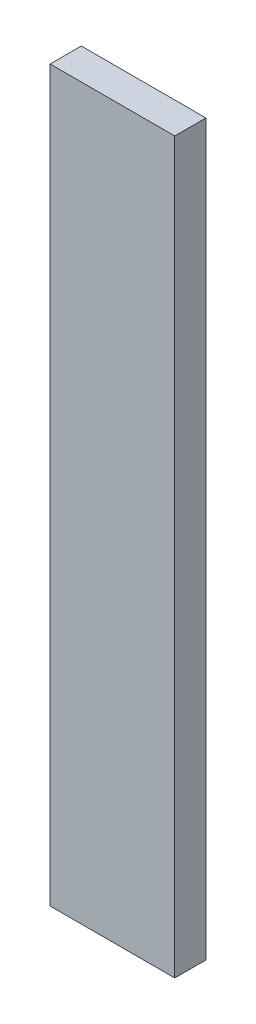
SolidWorks part; units mm, degrees
ref_plane "Front Plane" through (0, 0, 0) normal (0, 0, 1) x (1, 0, 0)
ref_plane "Top Plane" through (0, 0, 0) normal (0, 1, 0) x (1, 0, 0)
ref_plane "Right Plane" through (0, 0, 0) normal (1, 0, 0) x (0, 0, -1)
sketch "Sketch1" plane through (0, 0, 0) normal (0, 1, 0) x (1, 0, 0)
  line L1 (-20, -5) -> (20, -5)
  line L2 (-20, -5) -> (-20, 5)
  line L3 (-20, 5) -> (20, 5)
  line L4 (20, -5) -> (20, 5)
  line L5 (-20, -5) -> (20, 5) construction
  line L6 (-20, 5) -> (20, -5) construction
  point P0 (0, 0)
  dimension "D1" = 40
  dimension "D2" = 10
extrude "Boss-Extrude1" add sketch "Sketch1" along normal blind 234 contours L3 L4 L1 L2
